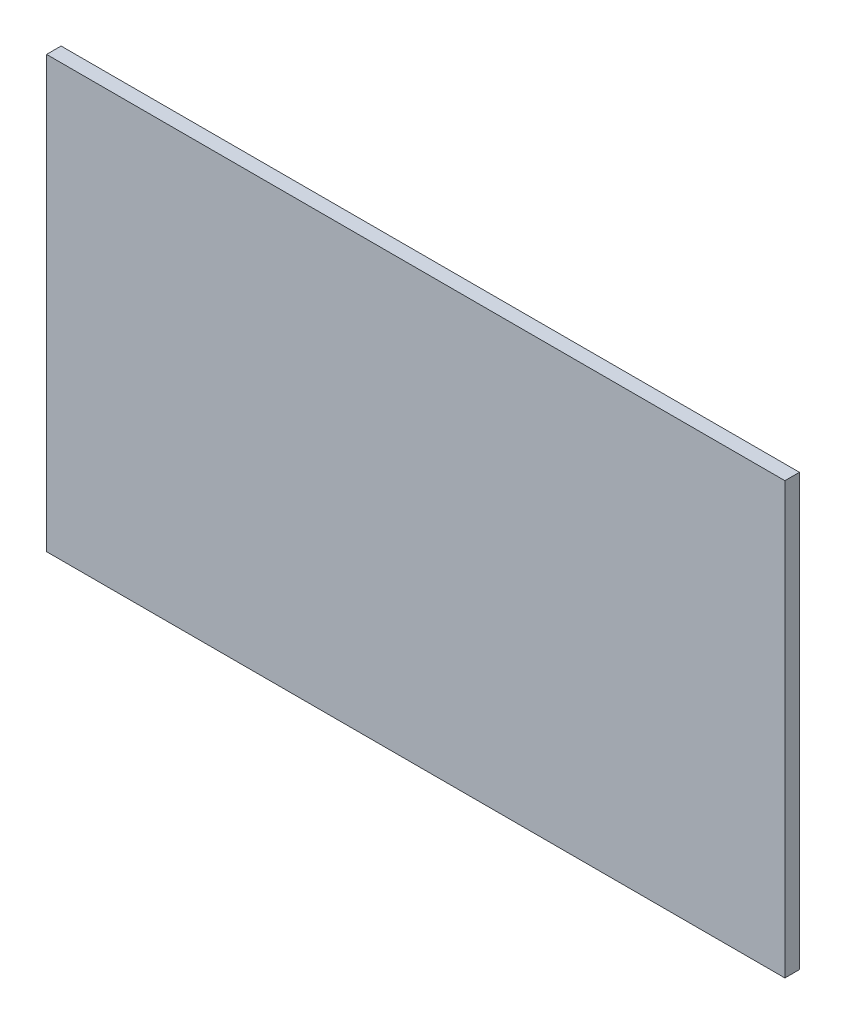
SolidWorks part; units mm, degrees
ref_plane "Front Plane" through (0, 0, 0) normal (0, 0, 1) x (1, 0, 0)
ref_plane "Top Plane" through (0, 0, 0) normal (0, 1, 0) x (1, 0, 0)
ref_plane "Right Plane" through (0, 0, 0) normal (1, 0, 0) x (0, 0, -1)
sketch "Sketch1" plane through (0, 0, 0) normal (0, 0, 1) x (1, 0, 0)
  line L1 (0, 0) -> (152.4, 0)
  line L2 (0, 0) -> (0, -88.9)
  line L3 (0, -88.9) -> (152.4, -88.9)
  line L4 (152.4, 0) -> (152.4, -88.9)
  dimension "D1" = 152.4
  dimension "D2" = 88.9
extrude "Boss-Extrude1" add sketch "Sketch1" along normal blind 2.9972
